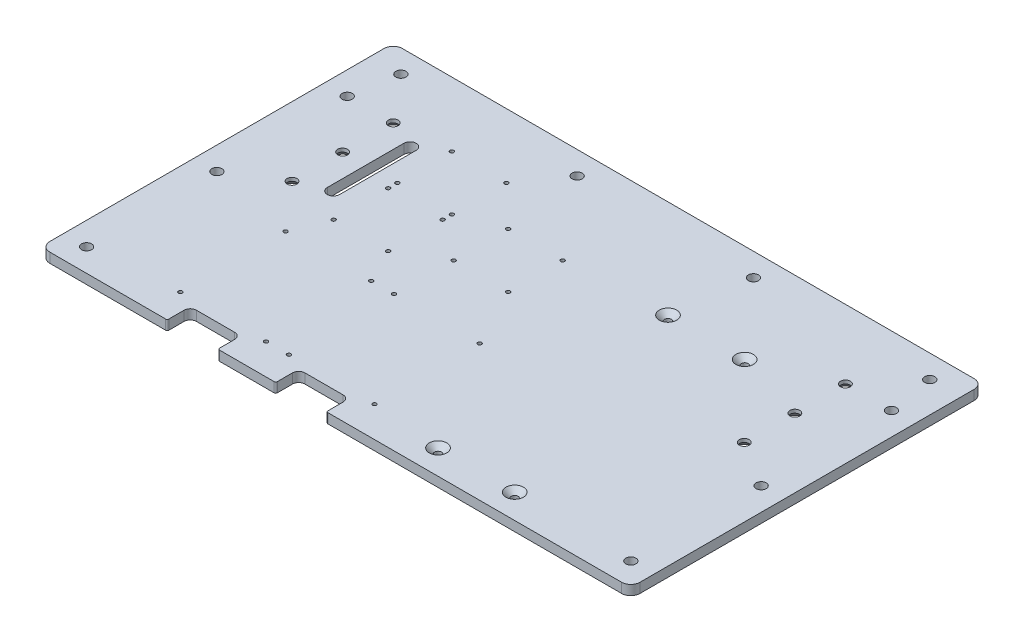
SolidWorks part; units mm, degrees
ref_plane "Front" through (0, 0, 0) normal (0, 0, 1) x (1, 0, 0)
ref_plane "Top" through (0, 0, 0) normal (0, 1, 0) x (1, 0, 0)
ref_plane "Right" through (0, 0, 0) normal (1, 0, 0) x (0, 0, -1)
sketch "Sketch1" plane through (0, 0, 0) normal (0, 1, 0) x (1, 0, 0)
  line L1 (-192.5, -100) -> (192.5, -100)
  line L2 (-192.5, -100) -> (-192.5, 100)
  line L3 (-192.5, 100) -> (192.5, 100)
  line L4 (192.5, -100) -> (192.5, 100)
  line L5 (0, 100) -> (0, -100) construction
  line L6 (-192.5, 0) -> (192.5, 0) construction
  point P0 (0, 0)
  dimension "D1" = 200
  dimension "D2" = 385
extrude "Boss-Extrude1" add sketch "Sketch1" along normal blind 6.35
hole_wizard "M6 Clearance Hole1" positions "Sketch7" profile "Sketch6" hole size "M6" standard "ANSI Metric" end condition through all
sketch "Sketch7" plane through (0, 6.35, 0) normal (0, 1, 0) x (1, 0, 0)
  line L0 (-192.5, 100) -> (-192.5, -100) construction
  line L1 (192.5, 100) -> (-192.5, 100) construction
  line L2 (-192.5, -100) -> (192.5, -100) construction
  point P0 (-177.5, 85)
  point P2 (-177.5, 0)
  point P4 (-177.5, -85)
  dimension "D1" = 15
  dimension "D2" = 15
  dimension "D3" = 15
  dimension "D4" = 100
sketch "Sketch6" plane through (-177.5, 6.35, -85) normal (1, 0, 0) x (0, 0, 1)
  line L0 (0, 0) -> (0, 6.35)
  line L1 (0, 6.35) -> (3.3, 6.35)
  line L2 (3.3, 6.35) -> (3.3, 0)
  line L5 (3.3, 0) -> (0, 0)
  line L11 (0, -6.35) -> (0, 107.95) construction
  dimension "Thru Hole Dia." = 6.6
  dimension "Thru Hole Depth" = 6.35
mirror "Mirror1" about plane through (0, 0, 0) normal (1, 0, 0) of "M6 Clearance Hole1"
hole_wizard "CSK for M6 Flat Head Machine Screw1" positions "Sketch9" profile "Sketch8" countersink size "M6" standard "ANSI Metric" end condition through all
sketch "Sketch9" plane through (0, 0, 0) normal (0, -1, 0) x (-1, 0, 0)
  line L0 (-192.5, -100) -> (-192.5, 100) construction
  line L1 (192.5, 100) -> (192.5, -100) construction
  point P0 (-147.5, 85)
  point P2 (-147.5, 52)
  point P4 (-147.5, 19)
  point P6 (147.5, 85)
  point P8 (147.5, 19)
  point P14 (147.5, 52)
  dimension "D1" = 33
  dimension "D2" = 33
  dimension "D3" = 52
  dimension "D4" = 45
  dimension "D5" = 45
sketch "Sketch8" plane through (147.5, 0, -85) normal (1, 0, 0) x (0, 0, -1)
  line L0 (0, 0) -> (0, 6.35)
  line L1 (0, 6.35) -> (3.2, 6.35)
  line L2 (3.2, 6.35) -> (3.2, 4.1)
  line L3 (3.2, 4.1) -> (7.3, 0)
  line L5 (7.3, 0) -> (0, 0)
  line L6 (-3.2, 4.1) -> (-7.3, 0) construction
  line L11 (0, -6.35) -> (0, 107.95) construction
  dimension "Thru Hole Dia." = 6.4
  dimension "Thru Hole Depth" = 6.35
  dimension "Near C'Sink Dia." = 14.6
  dimension "Near C'Sink Angle" = 90
hole_wizard "M3x0.5 Tapped Hole1" positions "Sketch11" profile "Sketch10" tap size "M3x0.5" standard "ANSI Metric"
sketch "Sketch11" plane through (0, 0, 0) normal (0, -1, 0) x (-1, 0, 0)
  line L0 (192.5, -100) -> (-192.5, -100) construction
  line L1 (76.6463, 52.44) -> (76.6463, 88) construction
  line L2 (76.6463, 88) -> (112.2063, 88) construction
  line L3 (112.2063, 88) -> (112.2063, 52.44) construction
  line L4 (112.2063, 52.44) -> (76.6463, 52.44) construction
  line L6 (76.6463, 10.88) -> (76.6463, 46.44) construction
  line L7 (76.6463, 46.44) -> (112.2063, 46.44) construction
  line L8 (112.2063, 46.44) -> (112.2063, 10.88) construction
  line L9 (112.2063, 10.88) -> (76.6463, 10.88) construction
  line L10 (-192.5, 100) -> (192.5, 100) construction
  point P0 (-5.3174, -80)
  point P2 (50.5626, -80)
  point P4 (65.433, -80)
  point P6 (121.313, -80)
  point P8 (121.313, -11.42)
  point P10 (65.433, -11.42)
  point P12 (50.5626, -11.42)
  point P14 (-5.3174, -11.42)
  point P16 (76.6463, 52.44)
  point P24 (76.6463, 88)
  point P26 (112.2063, 52.44)
  point P28 (112.2063, 88)
  point P30 (76.6463, 46.44)
  point P32 (112.2063, 46.44)
  point P34 (112.2063, 10.88)
  point P36 (76.6463, 10.88)
  dimension "D1" = 20
  dimension "D2" = 68.58
  dimension "D3" = 55.88
  dimension "D4" = 55.88
  dimension "D5" = 6
  dimension "D6" = 12
  dimension "D8" = 35.56
sketch "Sketch10" plane through (5.3174, 0, 80) normal (1, 0, 0) x (0, 0, -1)
  line L0 (0, 0) -> (0, 8.2511)
  line L1 (0, 8.2511) -> (1.25, 7.5)
  line L2 (1.25, 7.5) -> (1.25, 0)
  line L5 (1.25, 0) -> (0, 0)
  line L10 (0, 8.2511) -> (-1.25, 7.5) construction
  line L11 (0, -6.35) -> (0, 107.95) construction
  dimension "Tap Drill Dia." = 2.5
  dimension "Tap Drill Depth" = 7.5
  dimension "Drill Angle" = 118
cosmetic thread "Hole Thread1" parameters "D1"=6, "D2"=3
cosmetic thread "Hole Thread2" parameters "D1"=6, "D2"=3
cosmetic thread "Hole Thread3" parameters "D1"=6, "D2"=3
cosmetic thread "Hole Thread4" parameters "D1"=6, "D2"=3
cosmetic thread "Hole Thread5" parameters "D1"=6, "D2"=3
cosmetic thread "Hole Thread6" parameters "D1"=6, "D2"=3
cosmetic thread "Hole Thread7" parameters "D1"=6, "D2"=3
cosmetic thread "Hole Thread8" parameters "D1"=6, "D2"=3
cosmetic thread "Hole Thread9" parameters "D1"=6, "D2"=3
cosmetic thread "Hole Thread10" parameters "D1"=6, "D2"=3
cosmetic thread "Hole Thread11" parameters "D1"=6, "D2"=3
cosmetic thread "Hole Thread12" parameters "D1"=6, "D2"=3
cosmetic thread "Hole Thread13" parameters "D1"=6, "D2"=3
cosmetic thread "Hole Thread14" parameters "D1"=6, "D2"=3
cosmetic thread "Hole Thread15" parameters "D1"=6, "D2"=3
cosmetic thread "Hole Thread16" parameters "D1"=6, "D2"=3
hole_wizard "CSK for M4 Flat Head Machine Screw1" positions "Sketch13" profile "Sketch12" countersink size "M4" standard "ANSI Metric" end condition through all
sketch "Sketch13" plane through (0, 6.35, 0) normal (0, 1, 0) x (1, 0, 0)
  circle A0 centre (147.5, 19) radius 3.2 construction
  point P0 (50.75, -84)
  point P2 (100.75, -84)
  point P4 (50.75, 66)
  point P6 (100.75, 66)
  dimension "D1" = 50
  dimension "D2" = 150
  dimension "D3" = 46.75
sketch "Sketch12" plane through (50.75, 6.35, 84) normal (1, 0, 0) x (0, 0, 1)
  line L0 (0, 0) -> (0, 6.35)
  line L1 (0, 6.35) -> (2.25, 6.35)
  line L2 (2.25, 6.35) -> (2.25, 3.45)
  line L3 (2.25, 3.45) -> (5.7, 0)
  line L5 (5.7, 0) -> (0, 0)
  line L6 (-2.25, 3.45) -> (-5.7, 0) construction
  line L11 (0, -6.35) -> (0, 107.95) construction
  dimension "Thru Hole Dia." = 4.5
  dimension "Thru Hole Depth" = 6.35
  dimension "Near C'Sink Dia." = 11.4
  dimension "Near C'Sink Angle" = 90
hole_wizard "M3x0.5 Tapped Hole2" positions "Sketch15" profile "Sketch14" tap size "M3x0.5" standard "ANSI Metric" end condition through all
sketch "Sketch15" plane through (0, 0, 0) normal (0, -1, 0) x (-1, 0, 0)
  line L0 (14.5067, 26.9751) -> (14.5067, 62.5351) construction
  line L1 (14.5067, 62.5351) -> (50.0667, 62.5351) construction
  line L2 (50.0667, 62.5351) -> (50.0667, 26.9751) construction
  line L3 (50.0667, 26.9751) -> (14.5067, 26.9751) construction
  point P0 (14.5067, 62.5351)
  point P2 (50.0667, 62.5351)
  point P4 (50.0667, 26.9751)
  point P6 (14.5067, 26.9751)
  dimension "D1" = 35.56
sketch "Sketch14" plane through (-14.5067, 0, -62.5351) normal (1, 0, 0) x (0, 0, -1)
  line L0 (0, 0) -> (0, 6.35)
  line L1 (0, 6.35) -> (1.25, 6.35)
  line L2 (1.25, 6.35) -> (1.25, 0)
  line L5 (1.25, 0) -> (0, 0)
  line L11 (0, -6.35) -> (0, 107.95) construction
  dimension "Thru Tap Drill Dia." = 2.5
  dimension "Thru Tap Drill Depth" = 6.35
cosmetic thread "Hole Thread17" parameters "D2"=3
cosmetic thread "Hole Thread18" parameters "D2"=3
cosmetic thread "Hole Thread19" parameters "D2"=3
cosmetic thread "Hole Thread20" parameters "D2"=3
sketch "Sketch16" plane through (0, 0, 0) normal (0, -1, 0) x (1, 0, 0)
  line L0 (-128.5, -27) -> (-128.5, -77) construction
  line L1 (-124.5, -27) -> (-124.5, -77)
  line L2 (-132.5, -27) -> (-132.5, -77)
  line L3 (-147.5, -52) -> (-128.5, -52) construction
  arc A0 (-124.5, -27) -> (-132.5, -27) centre (-128.5, -27) ccw
  arc A1 (-132.5, -77) -> (-124.5, -77) centre (-128.5, -77) ccw
  circle A2 centre (-147.5, -52) radius 7.3 construction
  point P2 (-128.5, -52)
  dimension "D2" = 4
  dimension "D1" = 15
  dimension "D3" = 50
extrude "Cut-Extrude1" cut sketch "Sketch16" against normal through all
sketch "Sketch17" plane through (0, 0, 0) normal (0, -1, 0) x (1, 0, 0)
  line L0 (-105.873, 89) -> (-80.873, 89) construction
  line L1 (-105.873, 93) -> (-80.873, 93)
  line L2 (-105.873, 85) -> (-80.873, 85)
  line L3 (-35.1226, 89) -> (-10.1226, 89) construction
  line L4 (-35.1226, 93) -> (-10.1226, 93)
  line L5 (-35.1226, 85) -> (-10.1226, 85)
  line L6 (-121.313, 80) -> (-65.433, 80) construction
  line L7 (-50.5626, 80) -> (5.3174, 80) construction
  line L8 (-22.6226, 80) -> (-22.6226, 89) construction
  line L9 (-93.373, 80) -> (-93.373, 89) construction
  line L11 (-192.5, 100) -> (192.5, 100) construction
  arc A0 (-105.873, 93) -> (-105.873, 85) centre (-105.873, 89) ccw
  arc A1 (-80.873, 85) -> (-80.873, 93) centre (-80.873, 89) ccw
  arc A2 (-35.1226, 93) -> (-35.1226, 85) centre (-35.1226, 89) ccw
  arc A3 (-10.1226, 85) -> (-10.1226, 93) centre (-10.1226, 89) ccw
  point P2 (-93.373, 89)
  point P8 (-22.6226, 89)
  dimension "D1" = 4
  dimension "D3" = 7
  dimension "D2" = 25
extrude "Cut-Extrude2" cut sketch "Sketch17" against normal through all
sketch "Sketch18" plane through (0, 0, 0) normal (0, -1, 0) x (1, 0, 0)
  line L0 (-192.5, 100) -> (192.5, 100) construction
  line L1 (-6.1226, 89) -> (-39.1226, 89)
  line L2 (-6.1226, 89) -> (-6.1226, 100)
  line L3 (-6.1226, 100) -> (-39.1226, 100)
  line L4 (-39.1226, 89) -> (-39.1226, 100)
  line L6 (-76.873, 89) -> (-109.873, 89)
  line L7 (-76.873, 89) -> (-76.873, 100)
  line L8 (-76.873, 100) -> (-109.873, 100)
  line L9 (-109.873, 89) -> (-109.873, 100)
  arc A0 (-10.1226, 85) -> (-10.1226, 93) centre (-10.1226, 89) ccw construction
  arc A1 (-35.1226, 93) -> (-35.1226, 85) centre (-35.1226, 89) ccw construction
  arc A2 (-80.873, 85) -> (-80.873, 93) centre (-80.873, 89) ccw construction
  arc A3 (-105.873, 93) -> (-105.873, 85) centre (-105.873, 89) ccw construction
extrude "Cut-Extrude3" cut sketch "Sketch18" against normal through all
fillet "Fillet2" radius 1 4 edges at (-109.873, 3.175, 100) (-76.873, 3.175, 100) (-39.1226, 3.175, 100) (-6.1226, 3.175, 100)
sketch "Sketch19" plane through (0, 0, -100) normal (0, 0, -1) x (-1, 0, 0)
  line L4 (-192.5, 0) -> (192.5, 0)
  line L5 (192.5, 0) -> (192.5, 6.35)
  line L6 (192.5, 6.35) -> (-192.5, 6.35)
  line L7 (-192.5, 6.35) -> (-192.5, 0)
  line L8 (-192.5, 0) -> (192.5, 0)
  line L9 (192.5, 0) -> (192.5, 6.35)
  line L10 (192.5, 6.35) -> (-192.5, 6.35)
  line L11 (-192.5, 6.35) -> (-192.5, 0)
  dimension "D1" = 0
extrude "Boss-Extrude2" add sketch "Sketch19" along normal blind 30
hole_wizard "M6 Clearance Hole2" positions "Sketch23" profile "Sketch22" hole size "M6" standard "ANSI Metric" end condition through all
sketch "Sketch23" plane through (0, 0, 0) normal (0, -1, 0) x (-1, 0, 0)
  line L0 (-172.5, 115) -> (-57.5, 115) construction
  line L1 (-57.5, 115) -> (57.5, 115) construction
  line L2 (57.5, 115) -> (172.5, 115) construction
  line L7 (0, 115) -> (0, 130) construction
  line L8 (-192.5, 130) -> (192.5, 130) construction
  point P0 (-172.5, 115)
  point P2 (172.5, 115)
  point P4 (-57.5, 115)
  point P6 (57.5, 115)
  dimension "D1" = 115
  dimension "D2" = 15
sketch "Sketch22" plane through (172.5, 0, -115) normal (1, 0, 0) x (0, 0, -1)
  line L0 (0, 0) -> (0, 6.35)
  line L1 (0, 6.35) -> (3.3, 6.35)
  line L2 (3.3, 6.35) -> (3.3, 0)
  line L5 (3.3, 0) -> (0, 0)
  line L11 (0, -6.35) -> (0, 107.95) construction
  dimension "Thru Hole Dia." = 6.6
  dimension "Thru Hole Depth" = 6.35
fillet "Fillet3" radius 6 4 edges at (-192.5, 3.175, 100) (-192.5, 3.175, -130) (192.5, 3.175, 100) (192.5, 3.175, -130)
